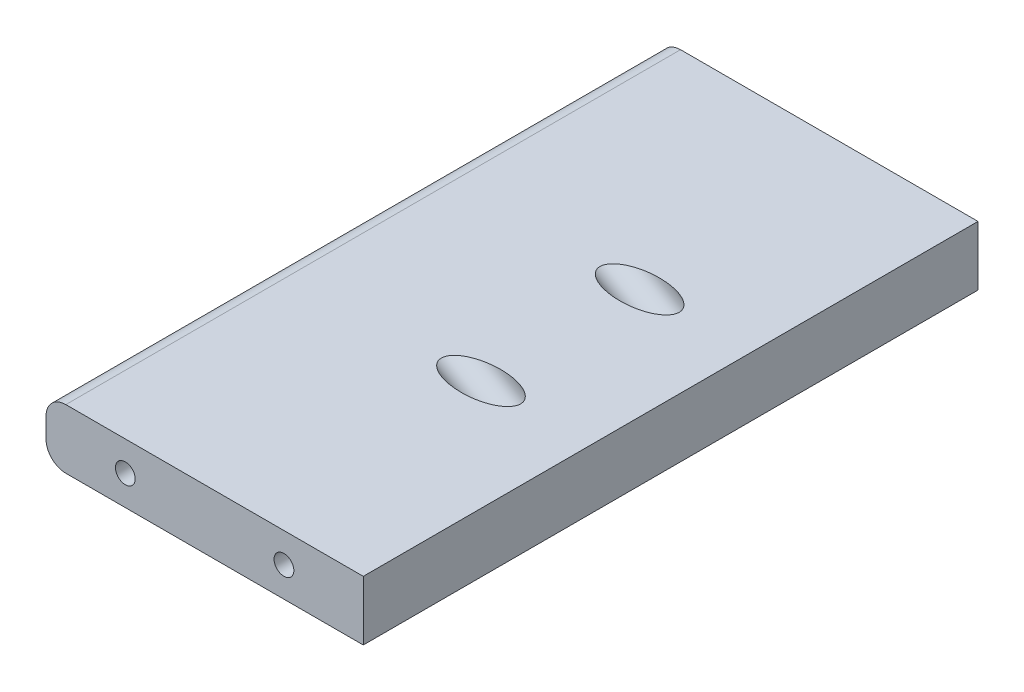
SolidWorks part; units mm, degrees
material "Mahogany"
ref_plane "Front Plane" through (0, 0, 0) normal (0, 0, 1) x (1, 0, 0)
ref_plane "Top Plane" through (0, 0, 0) normal (0, 1, 0) x (1, 0, 0)
ref_plane "Right Plane" through (0, 0, 0) normal (1, 0, 0) x (0, 0, -1)
sketch "Sketch1" plane through (0, 0, 0) normal (0, 0, 1) x (1, 0, 0)
  line L0 (44.45, 9.525) -> (50.8, 9.525)
  line L1 (-44.45, -9.525) -> (44.45, -9.525)
  line L2 (-50.8, -3.175) -> (-50.8, 3.175)
  line L3 (-44.45, 9.525) -> (44.45, 9.525)
  line L4 (50.8, -3.175) -> (50.8, 3.175)
  line L5 (-50.8, -9.525) -> (50.8, 9.525) construction
  line L6 (-50.8, 9.525) -> (50.8, -9.525) construction
  line L7 (50.8, 9.525) -> (50.8, 3.175)
  line L8 (44.45, -9.525) -> (50.8, -9.525)
  line L9 (50.8, -9.525) -> (50.8, -3.175)
  arc A2 (-50.8, -3.175) -> (-44.45, -9.525) centre (-44.45, -3.175) ccw
  arc A3 (-44.45, 9.525) -> (-50.8, 3.175) centre (-44.45, 3.175) ccw
  point P0 (0, 0)
  dimension "D1" = 19.05
  dimension "D2" = 101.6
extrude "Boss-Extrude1" add sketch "Sketch1" along normal mid plane 196.85
sketch "Sketch2" plane through (0, 0, 98.425) normal (0, 0, 1) x (1, 0, 0)
  line L0 (-25.4, -997.4935) -> (-25.4, 49002.5065) construction
  line L1 (25.4, -998.0764) -> (25.4, 49001.9236) construction
  line L2 (0, -55) -> (0, 55) construction
  line L3 (55, 0) -> (-55, 0) construction
  circle A0 centre (-25.4, 0) radius 3.175
  circle A1 centre (25.4, 0) radius 3.175
  dimension "D3" = 6.35
  dimension "D4" = 6.35
  dimension "D1" = 25.4
  dimension "D2" = 25.4
extrude "Cut-Extrude1" cut sketch "Sketch2" against normal blind 12.7
ref_plane "Plane1" through (-37.4619, 21.6287, 0) normal (0.866, -0.5, 0) x (0, 0, -1)
sketch "Sketch3" plane through (-37.4619, 21.6287, 0) normal (0.866, -0.5, 0) x (0, 0, -1)
  line L0 (0, -1000) -> (0, 49000) construction
  line L1 (-25.4, -935.3288) -> (-25.4, 49064.6712) construction
  line L2 (25.4, -941.2211) -> (25.4, 49058.7789) construction
  line L3 (-1106.0612, 15.9823) -> (48893.9388, 15.9823) construction
  circle A0 centre (-25.4, 15.9823) radius 6.35
  circle A1 centre (25.4, 15.9823) radius 6.35
  dimension "D3" = 12.7
  dimension "D4" = 12.7
  dimension "D1" = 50.8
  dimension "D2" = 25.4
extrude "Cut-Extrude2" cut sketch "Sketch3" along normal blind 66.04
mirror "Mirror1" about plane through (0, 0, 0) normal (0, 0, 1) of "Cut-Extrude1"
